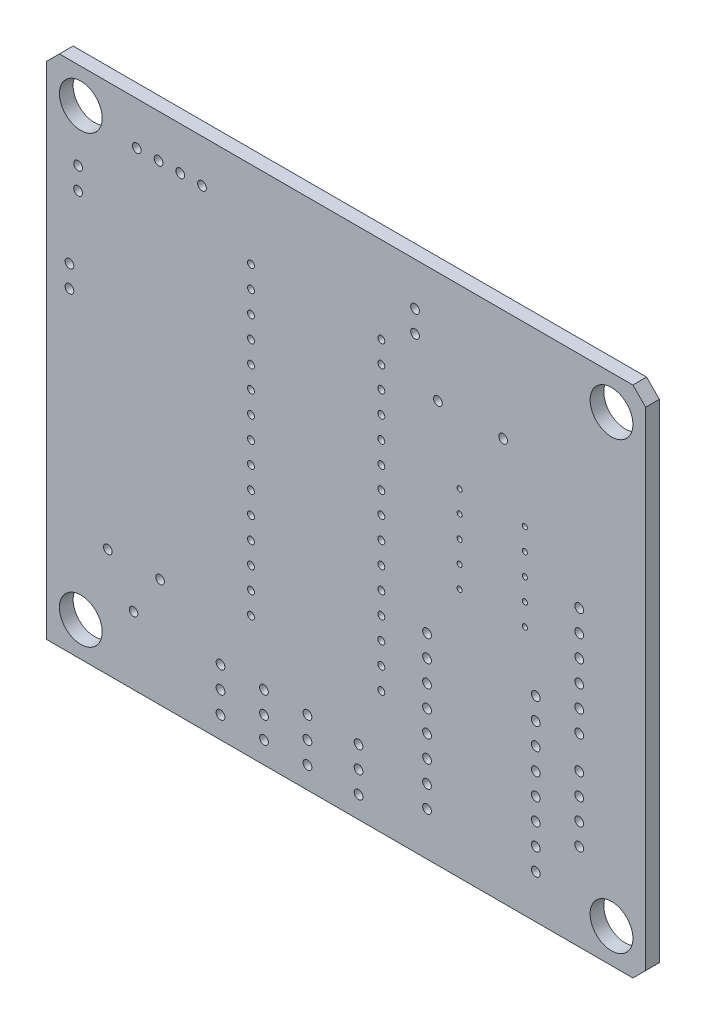
SolidWorks part; units mm, degrees
ref_plane "Front Plane" through (0, 0, 0) normal (0, 0, 1) x (1, 0, 0)
ref_plane "Top Plane" through (0, 0, 0) normal (0, 1, 0) x (1, 0, 0)
ref_plane "Right Plane" through (0, 0, 0) normal (1, 0, 0) x (0, 0, -1)
ref_plane "Dielectric_Layer Layer 1" through (0, 0, 1.6) normal (0, 0, 1) x (1, 0, 0)
sketch "Sketch1" plane through (0, 0, 0) normal (0, 0, 1) x (1, 0, 0)
  line L7 (0, 0) -> (68.5, 0)
  line L8 (68.5, 0) -> (70, 1.5)
  line L9 (70, 1.5) -> (70, 58.5)
  line L10 (70, 58.5) -> (68.5, 60)
  line L11 (68.5, 60) -> (1.5, 60)
  line L12 (1.5, 60) -> (0, 58.5)
  line L13 (0, 58.5) -> (0, 0)
  line L14 (1.5, 4) -> (1.5852, 3.353)
  line L15 (1.5852, 3.353) -> (1.8349, 2.75)
  line L16 (1.8349, 2.75) -> (2.2322, 2.2322)
  line L17 (2.2322, 2.2322) -> (2.75, 1.8349)
  line L18 (2.75, 1.8349) -> (3.353, 1.5852)
  line L19 (3.353, 1.5852) -> (4, 1.5)
  line L20 (4, 1.5) -> (4.647, 1.5852)
  line L21 (4.647, 1.5852) -> (5.25, 1.8349)
  line L22 (5.25, 1.8349) -> (5.7678, 2.2322)
  line L23 (5.7678, 2.2322) -> (6.1651, 2.75)
  line L24 (6.1651, 2.75) -> (6.4148, 3.353)
  line L25 (6.4148, 3.353) -> (6.5, 4)
  line L26 (6.5, 4) -> (6.4786, 4.3263)
  line L27 (6.4786, 4.3263) -> (6.4148, 4.647)
  line L28 (6.4148, 4.647) -> (6.1651, 5.25)
  line L29 (6.1651, 5.25) -> (5.7678, 5.7678)
  line L30 (5.7678, 5.7678) -> (5.25, 6.1651)
  line L31 (5.25, 6.1651) -> (4.647, 6.4148)
  line L32 (4.647, 6.4148) -> (4, 6.5)
  line L33 (4, 6.5) -> (3.353, 6.4148)
  line L34 (3.353, 6.4148) -> (2.75, 6.1651)
  line L35 (2.75, 6.1651) -> (2.2322, 5.7678)
  line L36 (2.2322, 5.7678) -> (1.8349, 5.25)
  line L37 (1.8349, 5.25) -> (1.5852, 4.647)
  line L38 (1.5852, 4.647) -> (1.5, 4)
  line L39 (1.5, 56) -> (1.5852, 55.353)
  line L40 (1.5852, 55.353) -> (1.8349, 54.75)
  line L41 (1.8349, 54.75) -> (2.2322, 54.2322)
  line L42 (2.2322, 54.2322) -> (2.75, 53.8349)
  line L43 (2.75, 53.8349) -> (3.353, 53.5852)
  line L44 (3.353, 53.5852) -> (4, 53.5)
  line L45 (4, 53.5) -> (4.647, 53.5852)
  line L46 (4.647, 53.5852) -> (5.25, 53.8349)
  line L47 (5.25, 53.8349) -> (5.7678, 54.2322)
  line L48 (5.7678, 54.2322) -> (6.1651, 54.75)
  line L49 (6.1651, 54.75) -> (6.4148, 55.353)
  line L50 (6.4148, 55.353) -> (6.5, 56)
  line L51 (6.5, 56) -> (6.4786, 56.3263)
  line L52 (6.4786, 56.3263) -> (6.4148, 56.647)
  line L53 (6.4148, 56.647) -> (6.1651, 57.25)
  line L54 (6.1651, 57.25) -> (5.7678, 57.7678)
  line L55 (5.7678, 57.7678) -> (5.25, 58.1651)
  line L56 (5.25, 58.1651) -> (4.647, 58.4148)
  line L57 (4.647, 58.4148) -> (4, 58.5)
  line L58 (4, 58.5) -> (3.353, 58.4148)
  line L59 (3.353, 58.4148) -> (2.75, 58.1651)
  line L60 (2.75, 58.1651) -> (2.2322, 57.7678)
  line L61 (2.2322, 57.7678) -> (1.8349, 57.25)
  line L62 (1.8349, 57.25) -> (1.5852, 56.647)
  line L63 (1.5852, 56.647) -> (1.5, 56)
  line L64 (63.5, 4) -> (63.5852, 3.353)
  line L65 (63.5852, 3.353) -> (63.8349, 2.75)
  line L66 (63.8349, 2.75) -> (64.2322, 2.2322)
  line L67 (64.2322, 2.2322) -> (64.75, 1.8349)
  line L68 (64.75, 1.8349) -> (65.353, 1.5852)
  line L69 (65.353, 1.5852) -> (66, 1.5)
  line L70 (66, 1.5) -> (66.647, 1.5852)
  line L71 (66.647, 1.5852) -> (67.25, 1.8349)
  line L72 (67.25, 1.8349) -> (67.7678, 2.2322)
  line L73 (67.7678, 2.2322) -> (68.1651, 2.75)
  line L74 (68.1651, 2.75) -> (68.4148, 3.353)
  line L75 (68.4148, 3.353) -> (68.5, 4)
  line L76 (68.5, 4) -> (68.4786, 4.3263)
  line L77 (68.4786, 4.3263) -> (68.4148, 4.647)
  line L78 (68.4148, 4.647) -> (68.1651, 5.25)
  line L79 (68.1651, 5.25) -> (67.7678, 5.7678)
  line L80 (67.7678, 5.7678) -> (67.25, 6.1651)
  line L81 (67.25, 6.1651) -> (66.647, 6.4148)
  line L82 (66.647, 6.4148) -> (66, 6.5)
  line L83 (66, 6.5) -> (65.353, 6.4148)
  line L84 (65.353, 6.4148) -> (64.75, 6.1651)
  line L85 (64.75, 6.1651) -> (64.2322, 5.7678)
  line L86 (64.2322, 5.7678) -> (63.8349, 5.25)
  line L87 (63.8349, 5.25) -> (63.5852, 4.647)
  line L88 (63.5852, 4.647) -> (63.5, 4)
  line L89 (63.5, 56) -> (63.5852, 55.353)
  line L90 (63.5852, 55.353) -> (63.8349, 54.75)
  line L91 (63.8349, 54.75) -> (64.2322, 54.2322)
  line L92 (64.2322, 54.2322) -> (64.75, 53.8349)
  line L93 (64.75, 53.8349) -> (65.353, 53.5852)
  line L94 (65.353, 53.5852) -> (66, 53.5)
  line L95 (66, 53.5) -> (66.647, 53.5852)
  line L96 (66.647, 53.5852) -> (67.25, 53.8349)
  line L97 (67.25, 53.8349) -> (67.7678, 54.2322)
  line L98 (67.7678, 54.2322) -> (68.1651, 54.75)
  line L99 (68.1651, 54.75) -> (68.4148, 55.353)
  line L100 (68.4148, 55.353) -> (68.5, 56)
  line L101 (68.5, 56) -> (68.4786, 56.3263)
  line L102 (68.4786, 56.3263) -> (68.4148, 56.647)
  line L103 (68.4148, 56.647) -> (68.1651, 57.25)
  line L104 (68.1651, 57.25) -> (67.7678, 57.7678)
  line L105 (67.7678, 57.7678) -> (67.25, 58.1651)
  line L106 (67.25, 58.1651) -> (66.647, 58.4148)
  line L107 (66.647, 58.4148) -> (66, 58.5)
  line L108 (66, 58.5) -> (65.353, 58.4148)
  line L109 (65.353, 58.4148) -> (64.75, 58.1651)
  line L110 (64.75, 58.1651) -> (64.2322, 57.7678)
  line L111 (64.2322, 57.7678) -> (63.8349, 57.25)
  line L112 (63.8349, 57.25) -> (63.5852, 56.647)
  line L113 (63.5852, 56.647) -> (63.5, 56)
extrude "Board_Outline 1" add sketch "Sketch1" along normal blind 1.6 separate body
sketch "Sketch2" plane through (0, 0, 0) normal (0, 0, 1) x (1, 0, 0)
  line L0 (6.5, 56) -> (6.4786, 56.3263) construction
  line L1 (6.4786, 56.3263) -> (6.4148, 56.647) construction
  line L2 (6.4148, 56.647) -> (6.1651, 57.25) construction
  line L3 (6.1651, 57.25) -> (5.7678, 57.7678) construction
  line L4 (5.7678, 57.7678) -> (5.25, 58.1651) construction
  line L5 (5.25, 58.1651) -> (4.647, 58.4148) construction
  line L6 (4.647, 58.4148) -> (4, 58.5) construction
  line L7 (4, 58.5) -> (3.353, 58.4148) construction
  line L8 (3.353, 58.4148) -> (2.75, 58.1651) construction
  line L9 (2.75, 58.1651) -> (2.2322, 57.7678) construction
  line L10 (2.2322, 57.7678) -> (1.8349, 57.25) construction
  line L11 (1.8349, 57.25) -> (1.5852, 56.647) construction
  line L12 (1.5852, 56.647) -> (1.5, 56) construction
  line L13 (1.5, 56) -> (1.5852, 55.353) construction
  line L14 (1.5852, 55.353) -> (1.8349, 54.75) construction
  line L15 (1.8349, 54.75) -> (2.2322, 54.2322) construction
  line L16 (2.2322, 54.2322) -> (2.75, 53.8349) construction
  line L17 (2.75, 53.8349) -> (3.353, 53.5852) construction
  line L18 (3.353, 53.5852) -> (4, 53.5) construction
  line L19 (4, 53.5) -> (4.647, 53.5852) construction
  line L20 (4.647, 53.5852) -> (5.25, 53.8349) construction
  line L21 (5.25, 53.8349) -> (5.7678, 54.2322) construction
  line L22 (5.7678, 54.2322) -> (6.1651, 54.75) construction
  line L23 (6.1651, 54.75) -> (6.4148, 55.353) construction
  line L24 (6.4148, 55.353) -> (6.5, 56) construction
  line L25 (6.1651, 57.25) -> (1.8349, 54.75) construction
  circle A0 centre (4, 56) radius 2.5
extrude "Board_Outline 2" cut sketch "Sketch2" along normal through all
sketch "Sketch3" plane through (0, 0, 0) normal (0, 0, 1) x (1, 0, 0)
  line L0 (68.5, 56) -> (68.4786, 56.3263) construction
  line L1 (68.4786, 56.3263) -> (68.4148, 56.647) construction
  line L2 (68.4148, 56.647) -> (68.1651, 57.25) construction
  line L3 (68.1651, 57.25) -> (67.7678, 57.7678) construction
  line L4 (67.7678, 57.7678) -> (67.25, 58.1651) construction
  line L5 (67.25, 58.1651) -> (66.647, 58.4148) construction
  line L6 (66.647, 58.4148) -> (66, 58.5) construction
  line L7 (66, 58.5) -> (65.353, 58.4148) construction
  line L8 (65.353, 58.4148) -> (64.75, 58.1651) construction
  line L9 (64.75, 58.1651) -> (64.2322, 57.7678) construction
  line L10 (64.2322, 57.7678) -> (63.8349, 57.25) construction
  line L11 (63.8349, 57.25) -> (63.5852, 56.647) construction
  line L12 (63.5852, 56.647) -> (63.5, 56) construction
  line L13 (63.5, 56) -> (63.5852, 55.353) construction
  line L14 (63.5852, 55.353) -> (63.8349, 54.75) construction
  line L15 (63.8349, 54.75) -> (64.2322, 54.2322) construction
  line L16 (64.2322, 54.2322) -> (64.75, 53.8349) construction
  line L17 (64.75, 53.8349) -> (65.353, 53.5852) construction
  line L18 (65.353, 53.5852) -> (66, 53.5) construction
  line L19 (66, 53.5) -> (66.647, 53.5852) construction
  line L20 (66.647, 53.5852) -> (67.25, 53.8349) construction
  line L21 (67.25, 53.8349) -> (67.7678, 54.2322) construction
  line L22 (67.7678, 54.2322) -> (68.1651, 54.75) construction
  line L23 (68.1651, 54.75) -> (68.4148, 55.353) construction
  line L24 (68.4148, 55.353) -> (68.5, 56) construction
  line L25 (66.647, 53.5852) -> (65.353, 58.4148) construction
  circle A0 centre (66, 56) radius 2.5
extrude "Board_Outline 3" cut sketch "Sketch3" along normal through all
sketch "Sketch4" plane through (0, 0, 0) normal (0, 0, 1) x (1, 0, 0)
  line L0 (68.5, 4) -> (68.4786, 4.3263) construction
  line L1 (68.4786, 4.3263) -> (68.4148, 4.647) construction
  line L2 (68.4148, 4.647) -> (68.1651, 5.25) construction
  line L3 (68.1651, 5.25) -> (67.7678, 5.7678) construction
  line L4 (67.7678, 5.7678) -> (67.25, 6.1651) construction
  line L5 (67.25, 6.1651) -> (66.647, 6.4148) construction
  line L6 (66.647, 6.4148) -> (66, 6.5) construction
  line L7 (66, 6.5) -> (65.353, 6.4148) construction
  line L8 (65.353, 6.4148) -> (64.75, 6.1651) construction
  line L9 (64.75, 6.1651) -> (64.2322, 5.7678) construction
  line L10 (64.2322, 5.7678) -> (63.8349, 5.25) construction
  line L11 (63.8349, 5.25) -> (63.5852, 4.647) construction
  line L12 (63.5852, 4.647) -> (63.5, 4) construction
  line L13 (63.5, 4) -> (63.5852, 3.353) construction
  line L14 (63.5852, 3.353) -> (63.8349, 2.75) construction
  line L15 (63.8349, 2.75) -> (64.2322, 2.2322) construction
  line L16 (64.2322, 2.2322) -> (64.75, 1.8349) construction
  line L17 (64.75, 1.8349) -> (65.353, 1.5852) construction
  line L18 (65.353, 1.5852) -> (66, 1.5) construction
  line L19 (66, 1.5) -> (66.647, 1.5852) construction
  line L20 (66.647, 1.5852) -> (67.25, 1.8349) construction
  line L21 (67.25, 1.8349) -> (67.7678, 2.2322) construction
  line L22 (67.7678, 2.2322) -> (68.1651, 2.75) construction
  line L23 (68.1651, 2.75) -> (68.4148, 3.353) construction
  line L24 (68.4148, 3.353) -> (68.5, 4) construction
  line L25 (63.8349, 2.75) -> (68.1651, 5.25) construction
  circle A0 centre (66, 4) radius 2.5
extrude "Board_Outline 4" cut sketch "Sketch4" along normal through all
sketch "Sketch5" plane through (0, 0, 0) normal (0, 0, 1) x (1, 0, 0)
  line L0 (6.5, 4) -> (6.4786, 4.3263) construction
  line L1 (6.4786, 4.3263) -> (6.4148, 4.647) construction
  line L2 (6.4148, 4.647) -> (6.1651, 5.25) construction
  line L3 (6.1651, 5.25) -> (5.7678, 5.7678) construction
  line L4 (5.7678, 5.7678) -> (5.25, 6.1651) construction
  line L5 (5.25, 6.1651) -> (4.647, 6.4148) construction
  line L6 (4.647, 6.4148) -> (4, 6.5) construction
  line L7 (4, 6.5) -> (3.353, 6.4148) construction
  line L8 (3.353, 6.4148) -> (2.75, 6.1651) construction
  line L9 (2.75, 6.1651) -> (2.2322, 5.7678) construction
  line L10 (2.2322, 5.7678) -> (1.8349, 5.25) construction
  line L11 (1.8349, 5.25) -> (1.5852, 4.647) construction
  line L12 (1.5852, 4.647) -> (1.5, 4) construction
  line L13 (1.5, 4) -> (1.5852, 3.353) construction
  line L14 (1.5852, 3.353) -> (1.8349, 2.75) construction
  line L15 (1.8349, 2.75) -> (2.2322, 2.2322) construction
  line L16 (2.2322, 2.2322) -> (2.75, 1.8349) construction
  line L17 (2.75, 1.8349) -> (3.353, 1.5852) construction
  line L18 (3.353, 1.5852) -> (4, 1.5) construction
  line L19 (4, 1.5) -> (4.647, 1.5852) construction
  line L20 (4.647, 1.5852) -> (5.25, 1.8349) construction
  line L21 (5.25, 1.8349) -> (5.7678, 2.2322) construction
  line L22 (5.7678, 2.2322) -> (6.1651, 2.75) construction
  line L23 (6.1651, 2.75) -> (6.4148, 3.353) construction
  line L24 (6.4148, 3.353) -> (6.5, 4) construction
  circle A0 centre (4, 4) radius 2.5
extrude "Board_Outline 5" cut sketch "Sketch5" along normal through all
sketch "Sketch6" plane through (0, 0, 0) normal (0, 0, 1) x (1, 0, 0)
  line L0 (10.541, 54.991) -> (18.161, 54.991) construction
  line L1 (0, 58.5) -> (0, 0) construction
  line L2 (0, 0) -> (68.5, 0) construction
  line L3 (3.683, 49.784) -> (3.683, 47.244) construction
  circle A93 centre (53.34, 46.99) radius 0.51
  circle A94 centre (45.72, 46.99) radius 0.51
  circle A95 centre (30.48, 7.62) radius 0.51
  circle A96 centre (30.48, 5.08) radius 0.51
  circle A97 centre (30.48, 2.54) radius 0.51
  circle A98 centre (25.4, 7.62) radius 0.51
  circle A99 centre (25.4, 5.08) radius 0.51
  circle A100 centre (25.4, 2.54) radius 0.51
  circle A101 centre (20.32, 7.62) radius 0.51
  circle A102 centre (20.32, 5.08) radius 0.51
  circle A103 centre (20.32, 2.54) radius 0.51
  circle A104 centre (48.26, 34.29) radius 0.3
  circle A105 centre (48.26, 39.37) radius 0.3
  circle A106 centre (55.88, 39.37) radius 0.3
  circle A107 centre (55.88, 31.75) radius 0.3
  circle A108 centre (55.88, 34.29) radius 0.3
  circle A109 centre (48.26, 31.75) radius 0.3
  circle A110 centre (48.26, 29.21) radius 0.3
  circle A111 centre (48.26, 36.83) radius 0.3
  circle A112 centre (55.88, 36.83) radius 0.3
  circle A113 centre (55.88, 29.21) radius 0.3
  circle A114 centre (44.45, 22.86) radius 0.51
  circle A115 centre (44.45, 20.32) radius 0.51
  circle A116 centre (44.45, 17.78) radius 0.51
  circle A117 centre (44.45, 15.24) radius 0.51
  circle A118 centre (44.45, 12.7) radius 0.51
  circle A119 centre (44.45, 10.16) radius 0.51
  circle A120 centre (44.45, 7.62) radius 0.51
  circle A121 centre (44.45, 5.08) radius 0.51
  circle A122 centre (57.15, 5.08) radius 0.51
  circle A123 centre (57.15, 7.62) radius 0.51
  circle A124 centre (57.15, 10.16) radius 0.51
  circle A125 centre (57.15, 12.7) radius 0.51
  circle A126 centre (57.15, 15.24) radius 0.51
  circle A127 centre (57.15, 17.78) radius 0.51
  circle A128 centre (57.15, 20.32) radius 0.51
  circle A129 centre (57.15, 22.86) radius 0.51
  circle A130 centre (43.05, 52.45) radius 0.51
  circle A131 centre (43.05, 54.99) radius 0.51
  circle A132 centre (62.23, 21.59) radius 0.51
  circle A133 centre (62.23, 24.13) radius 0.51
  circle A134 centre (62.23, 26.67) radius 0.51
  circle A135 centre (62.23, 29.21) radius 0.51
  circle A136 centre (62.23, 31.75) radius 0.51
  circle A137 centre (62.23, 34.29) radius 0.51
  circle A138 centre (36.45, 2.54) radius 0.51
  circle A139 centre (36.45, 5.08) radius 0.51
  circle A140 centre (36.45, 7.62) radius 0.51
  circle A141 centre (13.26, 12.7) radius 0.5
  circle A142 centre (10.16, 7.9) radius 0.5
  circle A143 centre (7.16, 12.7) radius 0.5
  circle A144 centre (2.67, 36.83) radius 0.51
  circle A145 centre (2.67, 39.37) radius 0.51
  circle A146 centre (3.683, 49.784) radius 0.51
  circle A147 centre (3.683, 47.244) radius 0.51
  circle A148 centre (62.23, 17.78) radius 0.51
  circle A149 centre (62.23, 15.24) radius 0.51
  circle A150 centre (62.23, 12.7) radius 0.51
  circle A151 centre (62.23, 10.16) radius 0.51
  circle A152 centre (39.11, 14.35) radius 0.405
  circle A153 centre (39.11, 16.89) radius 0.405
  circle A154 centre (39.11, 19.43) radius 0.405
  circle A155 centre (39.11, 21.97) radius 0.405
  circle A156 centre (39.11, 24.51) radius 0.405
  circle A157 centre (39.11, 27.05) radius 0.405
  circle A158 centre (39.11, 29.59) radius 0.405
  circle A159 centre (39.11, 32.13) radius 0.405
  circle A160 centre (39.11, 34.67) radius 0.405
  circle A161 centre (39.11, 37.21) radius 0.405
  circle A162 centre (39.11, 39.75) radius 0.405
  circle A163 centre (39.11, 42.29) radius 0.405
  circle A164 centre (39.11, 44.83) radius 0.405
  circle A165 centre (39.11, 47.37) radius 0.405
  circle A166 centre (39.11, 49.91) radius 0.405
  circle A167 centre (23.88, 49.91) radius 0.405
  circle A168 centre (23.88, 47.37) radius 0.405
  circle A169 centre (23.88, 44.83) radius 0.405
  circle A170 centre (23.88, 42.29) radius 0.405
  circle A171 centre (23.88, 39.75) radius 0.405
  circle A172 centre (23.88, 37.21) radius 0.405
  circle A173 centre (23.88, 34.67) radius 0.405
  circle A174 centre (23.88, 32.13) radius 0.405
  circle A175 centre (23.88, 29.59) radius 0.405
  circle A176 centre (23.88, 27.05) radius 0.405
  circle A177 centre (23.88, 24.51) radius 0.405
  circle A178 centre (23.88, 21.97) radius 0.405
  circle A179 centre (23.88, 19.43) radius 0.405
  circle A180 centre (23.88, 16.89) radius 0.405
  circle A181 centre (23.88, 14.35) radius 0.405
  circle A182 centre (10.541, 54.991) radius 0.51
  circle A183 centre (13.081, 54.991) radius 0.51
  circle A184 centre (15.621, 54.991) radius 0.51
  circle A185 centre (18.161, 54.991) radius 0.51
  point P0 (3.683, 48.514)
  point P1 (14.351, 54.991)
extrude "PTH" cut sketch "Sketch6" along normal through all
